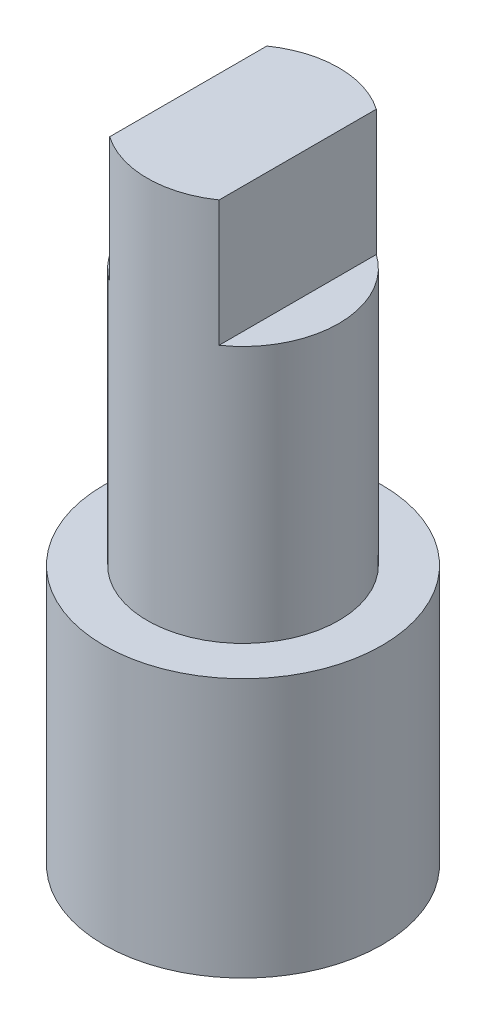
SolidWorks part; units mm, degrees
material "Brass"
ref_plane "Front Plane" through (0, 0, 0) normal (0, 0, 1) x (1, 0, 0)
ref_plane "Top Plane" through (0, 0, 0) normal (0, 1, 0) x (1, 0, 0)
ref_plane "Right Plane" through (0, 0, 0) normal (1, 0, 0) x (0, 0, -1)
sketch "Sketch1" plane through (0, 0, 0) normal (0, 1, 0) x (1, 0, 0)
  circle A0 centre (0, 0) radius 1.75
  dimension "D1" = 3.5
extrude "Boss-Extrude1" add sketch "Sketch1" along normal blind 11.738
sketch "Sketch2" plane through (0, 11.738, 0) normal (0, 1, 0) x (1, 0, 0)
  line L1 (-1, 1.75) -> (1, 1.75)
  line L2 (-1, 1.75) -> (-1, -1.75)
  line L3 (-1, -1.75) -> (1, -1.75)
  line L4 (1, 1.75) -> (1, -1.75)
  line L5 (-1, 1.75) -> (1, -1.75) construction
  line L6 (-1, -1.75) -> (1, 1.75) construction
  circle A0 centre (0, 0) radius 1.75 construction
  circle A1 centre (0, 0) radius 1.75
  point P0 (0, 0)
  circle M6 centre (0, 0) radius 1.75
  dimension "D1" = 2
extrude "Cut-Extrude1" cut sketch "Sketch2" against normal blind 2.3 contours L2 M6 | L4 M6
sketch "Sketch3" plane through (0, 0, 0) normal (0, -1, 0) x (1, 0, 0)
  circle A0 centre (0, 0) radius 2.54
  dimension "D1" = 5.08
extrude "Boss-Extrude2" add sketch "Sketch3" against normal blind 4.738
